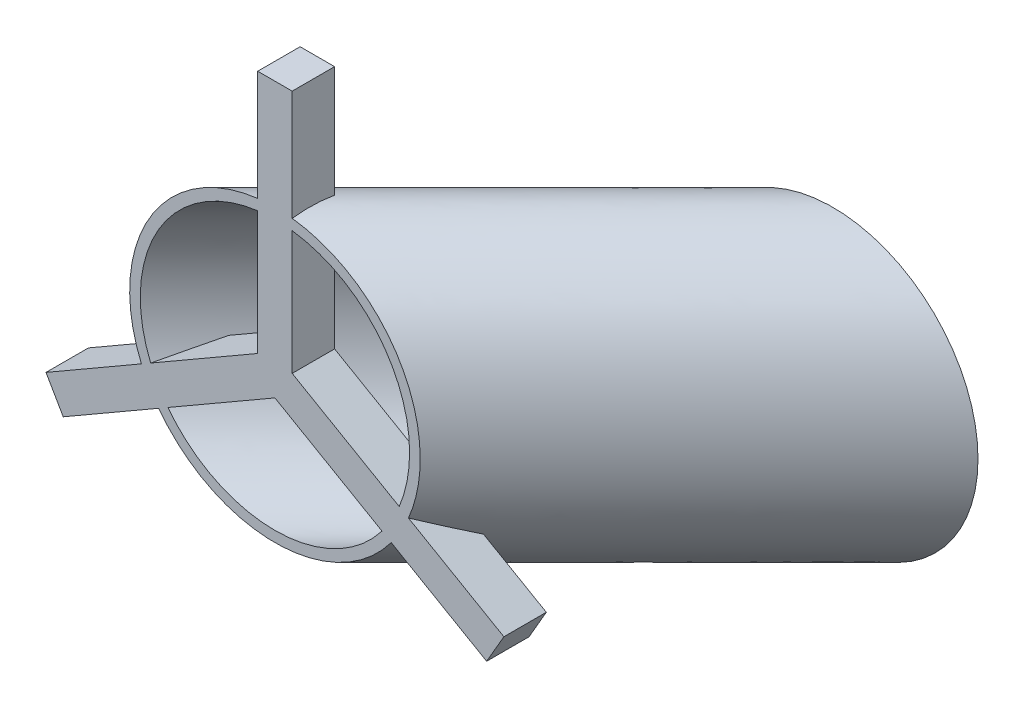
SolidWorks part; units mm, degrees
ref_plane "Plan de face" through (0, 0, 0) normal (0, 0, 1) x (1, 0, 0)
ref_plane "Plan de dessus" through (0, 0, 0) normal (0, 1, 0) x (1, 0, 0)
ref_plane "Plan de droite" through (0, 0, 0) normal (1, 0, 0) x (0, 0, -1)
sketch "Esquisse1" plane through (0, 0, 0) normal (0, 0, 1) x (1, 0, 0)
  circle A0 centre (0, 0) radius 12.7
  circle A1 centre (0, 0) radius 13.7
  dimension "D1" = 25.4
  dimension "D2" = 27.4
sketch "Esquisse2" plane through (0, 0, 0) normal (0, 1, 0) x (1, 0, 0)
  line L0 (0, 0) -> (26.3036, 26.3036)
  line L1 (-12.7, 0) -> (12.7, 0) construction
  dimension "D1" = 45
sweep "Balayage1" add profiles "Esquisse1" path "Esquisse2"
sketch "Esquisse3" plane through (0, 0, 0) normal (0, 0, 1) x (1, 0, 0)
  line L0 (1.6259, 0) -> (-1.6259, 0)
  line L1 (-1.6259, 0) -> (-1.6259, 23.9938)
  line L2 (-1.6259, 23.9938) -> (1.6259, 23.9938)
  line L3 (1.6259, 23.9938) -> (1.6259, 0)
  point P4 (0, 0)
extrude "Boss.-Extru.1" add sketch "Esquisse3" against normal blind 4
pattern_circular "Répétition circulaire1" count 3 over 360 about axis through (0, 0, 0) along (0, 0, 1) of "Boss.-Extru.1"
equation "\"diam_int\"=25.4"
equation "\"D1@Esquisse1\"=\"diam_int\""
equation "\"D2@Esquisse1\"=\"diam_int\"+2"
